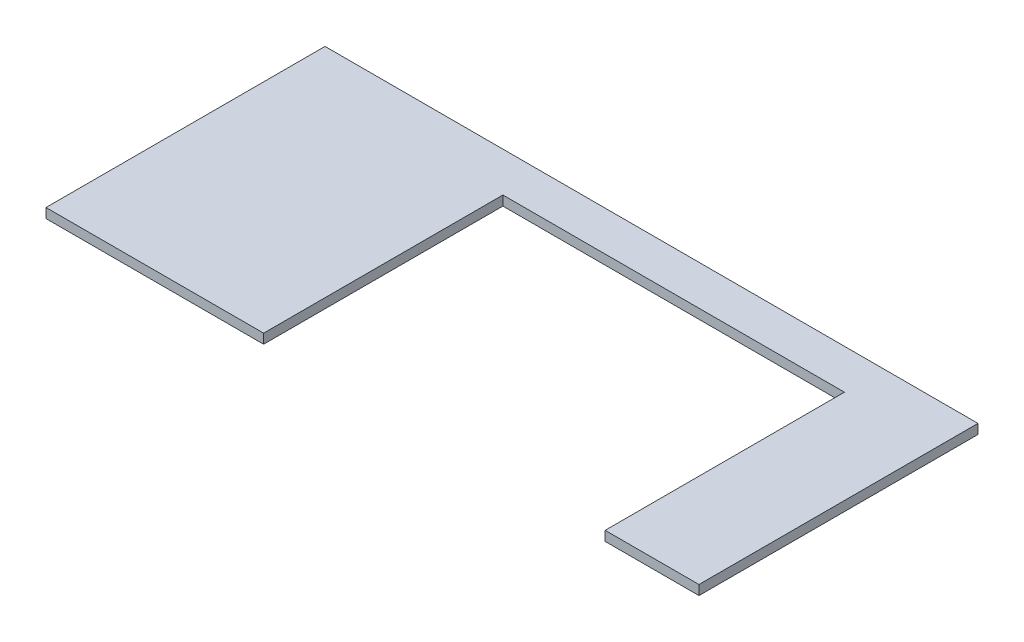
SolidWorks part; units mm, degrees
material "Oak"
ref_plane "Front Plane" through (0, 0, 0) normal (0, 0, 1) x (1, 0, 0)
ref_plane "Top Plane" through (0, 0, 0) normal (0, 1, 0) x (1, 0, 0)
ref_plane "Right Plane" through (0, 0, 0) normal (1, 0, 0) x (0, 0, -1)
sketch "Sketch1" plane through (0, 0, 0) normal (0, 1, 0) x (1, 0, 0)
  line L4 (1292.86, 0) -> (1292.86, 552.45)
  line L5 (1292.86, 552.45) -> (0, 552.45)
  line L7 (0, 0) -> (1292.86, 0)
  line L8 (0, 552.45) -> (0, 0)
  dimension "D1" = 1292.86
  dimension "D5" = 552.45
extrude "Boss-Extrude1" add sketch "Sketch1" against normal blind 19.05
sketch "Sketch4" plane through (0, 0, 0) normal (0, 1, 0) x (1, 0, 0)
  line L1 (430.8856, 473.71) -> (1107.0869, 473.71)
  line L2 (430.8856, 473.71) -> (430.8856, 0)
  line L4 (1107.0869, 473.71) -> (1107.0869, 0)
  line L5 (430.8856, 0) -> (1107.0869, 0)
  line L7 (0, 0) -> (1292.86, 0) construction
  dimension "D1" = 430.8856
  dimension "D2" = 676.2013
  dimension "D3" = 473.71
extrude "Cut-Extrude3" cut sketch "Sketch4" against normal through all
